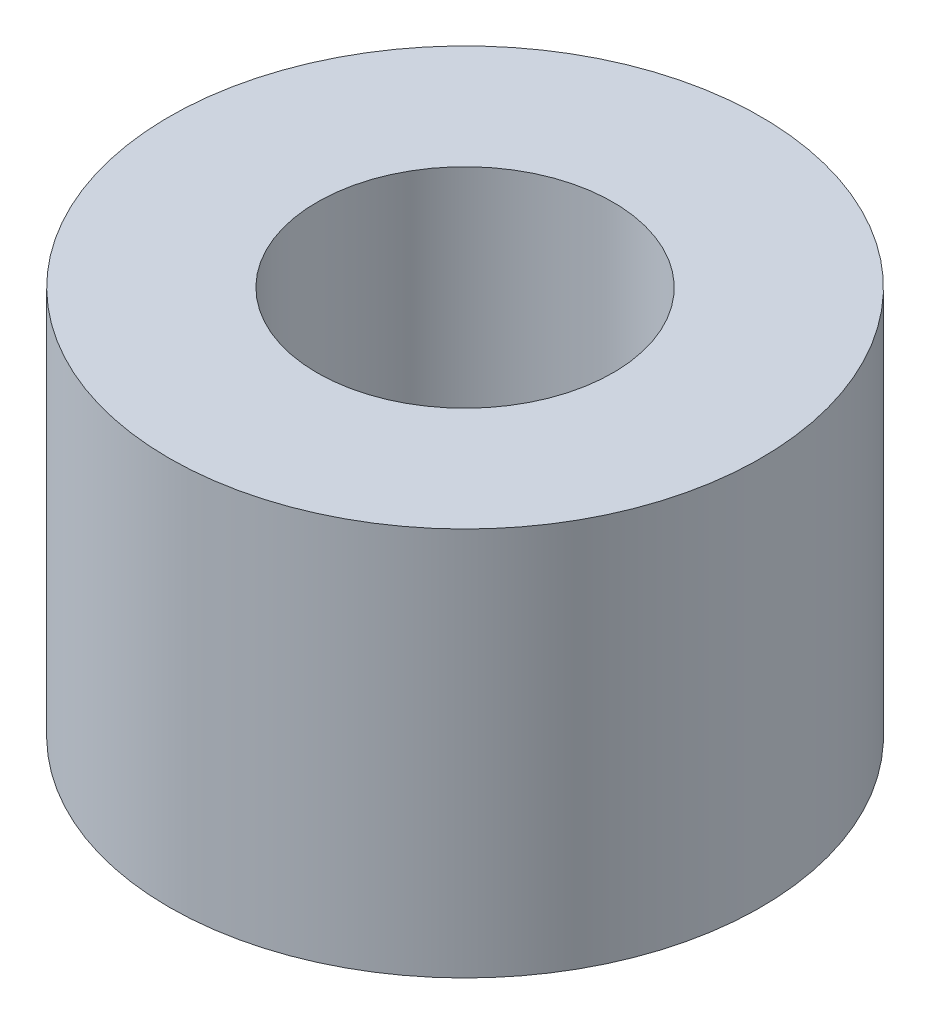
SolidWorks part; units mm, degrees
ref_plane "Front Plane" through (0, 0, 0) normal (0, 0, 1) x (1, 0, 0)
ref_plane "Top Plane" through (0, 0, 0) normal (0, 1, 0) x (1, 0, 0)
ref_plane "Right Plane" through (0, 0, 0) normal (1, 0, 0) x (0, 0, -1)
sketch "Sketch1" plane through (0, 0, 0) normal (0, 1, 0) x (1, 0, 0)
  circle A0 centre (0, 0) radius 1.75
  circle A1 centre (0, 0) radius 3.5
  dimension "D1" = 3.5
  dimension "D2" = 7
extrude "Boss-Extrude1" add sketch "Sketch1" along normal blind 4.6
